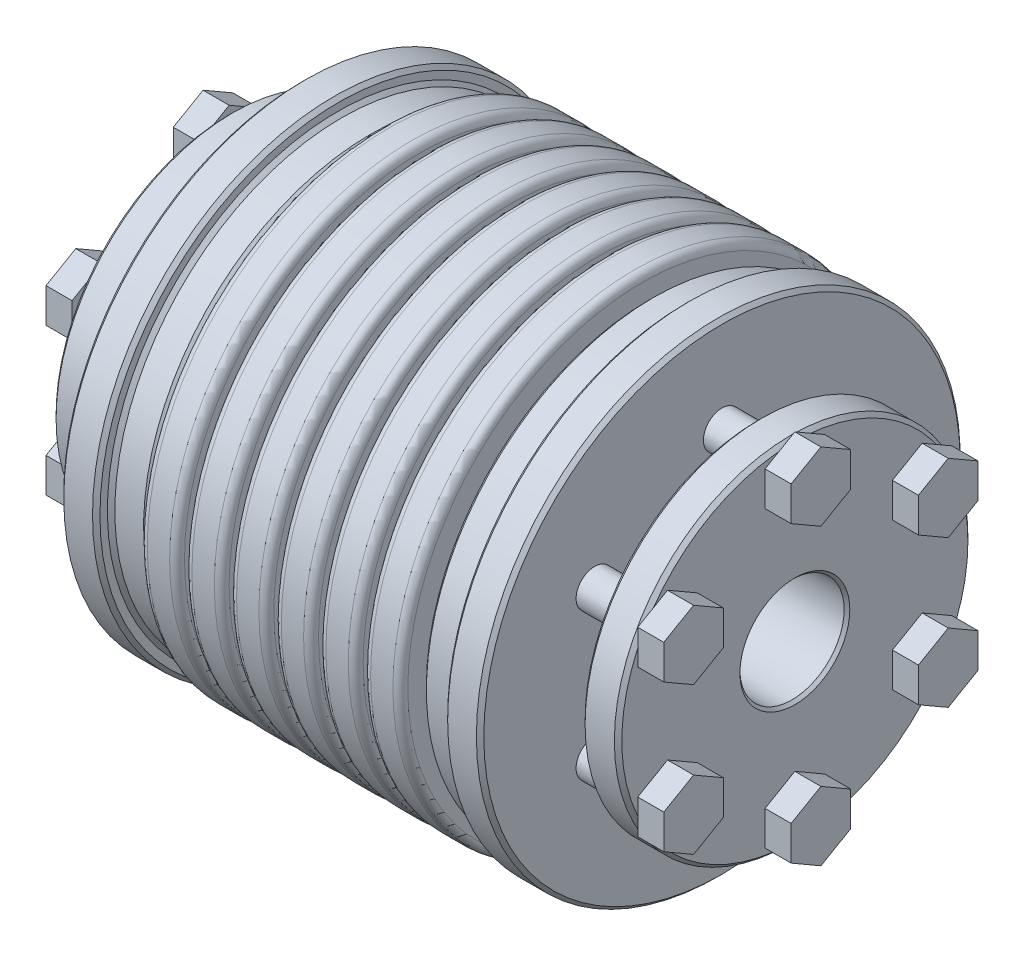
SolidWorks part; units mm, degrees
ref_plane "Front Plane" through (0, 0, 0) normal (0, 0, 1) x (1, 0, 0)
ref_plane "Top Plane" through (0, 0, 0) normal (0, 1, 0) x (1, 0, 0)
ref_plane "Right Plane" through (0, 0, 0) normal (1, 0, 0) x (0, 0, -1)
sketch "Sketch1" plane through (0, 0, 0) normal (1, 0, 0) x (0, 0, -1)
  circle A0 centre (0, 0) radius 32.5
  dimension "dim D" = 65
extrude "Boss-Extrude1" add sketch "Sketch1" along normal mid plane 76
sketch "Sketch2" plane through (38, 0, 0) normal (1, 0, 0) x (0, 0, -1)
  circle A0 centre (0, 0) radius 7
  dimension "dim d1" = 14
extrude "Cut-Extrude1" cut sketch "Sketch2" against normal blind 19
mirror "Mirror3" about plane through (0, 0, 0) normal (1, 0, 0) of "Cut-Extrude1"
chamfer "Chamfer1" distance 0.381 angle 45 4 edges at (-38, 0, -32.5) (38, 0, -32.5) (38, 0, -7) (-38, 0, -7)
ref_plane "L1" through (11, 0, 0) normal (1, 0, 0) x (0, 0, -1)
sketch "Sketch5" plane through (0, 0, 0) normal (1, 0, 0) x (0, 0, -1)
  line L0 (0, 7.381) -> (0, 32.5) construction
  circle A0 centre (0, 0) radius 7.381 construction
  circle A1 centre (0, 0) radius 19.9405
  circle A3 centre (0, 0) radius 32.5 construction
  point P9 (0, 19.9405)
extrude "Cut-Extrude2" cut sketch "Sketch5" against normal up to surface and the other way up to surface up to face at (-19, 0, -7) other way up to face at (19, 0, -7)
sketch "Sketch8" plane through (0, 0, 0) normal (0, 1, 0) x (1, 0, 0)
  line L0 (19, 19.9405) -> (-19, 19.9405) construction
  line L2 (-0.5, 21.9405) -> (0.5, 21.9405)
  line L3 (-0.5, 21.9405) -> (-0.5, 32.5)
  line L4 (-0.5, 32.5) -> (0.5, 32.5)
  line L5 (0, 21.9405) -> (0, 0) construction
  line L6 (0.5, 21.9405) -> (0.5, 32.5)
  line L7 (0, 0) -> (38, 0) construction
  line L8 (38, -32.119) -> (38, 32.119) construction
  line L9 (19, 7) -> (19, -7) construction
  line L10 (19, 7) -> (19, -7) construction
  line L11 (-38, -21.9405) -> (38, -21.9405) construction
  line L13 (0.5, 21.9405) -> (1.27, 21.9405) construction
  line L14 (-38, 32.119) -> (-38, -32.119) construction
  line L15 (5.5, 21.9405) -> (6.5, 21.9405)
  line L16 (5.5, 21.9405) -> (5.5, 32.5)
  line L17 (5.5, 32.5) -> (6.5, 32.5)
  line L18 (6.5, 21.9405) -> (6.5, 32.5)
  line L19 (11.5, 21.9405) -> (12.5, 21.9405)
  line L20 (11.5, 21.9405) -> (11.5, 32.5)
  line L21 (11.5, 32.5) -> (12.5, 32.5)
  line L22 (12.5, 21.9405) -> (12.5, 32.5)
  line L23 (17.5, 21.9405) -> (18.5, 21.9405)
  line L24 (17.5, 21.9405) -> (17.5, 32.5)
  line L25 (17.5, 32.5) -> (18.5, 32.5)
  line L26 (18.5, 21.9405) -> (18.5, 32.5)
  line L27 (-0.5, 21.9405) -> (5.5, 21.9405) construction
  line L28 (0, 0) -> (0, -21.9405) construction
  dimension "D2" = 4
  dimension "D1" = 1
  dimension "D3" = 2
  dimension "Dim L2" = 37
revolve "Cut-Revolve1" cut sketch "Sketch8" angle 360 about L7
mirror "Mirror2" about plane through (0, 0, 0) normal (1, 0, 0) of "Cut-Revolve1"
fillet "Fillet1" radius 1 14 edges at (0.5, 0, 32.5) (-0.5, 0, 32.5) (18.5, 0, 32.5) (17.5, 0, 32.5) (12.5, 0, 32.5) (11.5, 0, 32.5) (6.5, 0, 32.5) (5.5, 0, 32.5) (-17.5, 0, 32.5) (-12.5, 0, 32.5) (-11.5, 0, 32.5) (-6.5, 0, 32.5) (-5.5, 0, 32.5) (-18.5, 0, 32.5)
fillet "Fillet2" radius 0.25 14 edges at (-11.5, 0, 21.9405) (-5.5, 0, 21.9405) (0.5, 0, 21.9405) (6.5, 0, 21.9405) (12.5, 0, 21.9405) (18.5, 0, 21.9405) (17.5, 0, 21.9405) (11.5, 0, 21.9405) (5.5, 0, 21.9405) (-0.5, 0, 21.9405) (-6.5, 0, 21.9405) (-12.5, 0, 21.9405) (-17.5, 0, 21.9405) (-18.5, 0, 21.9405)
sketch "Sketch9" plane through (0, 0, 0) normal (0, 0, 1) x (1, 0, 0)
  line L0 (18.5, 30.5) -> (23.3563, 30.5)
  line L1 (18.5, 31.5) -> (18.5, -31.5) construction
  line L2 (23.3563, 30.5) -> (23.3563, 32.5)
  line L3 (37.619, 32.5) -> (19.5, 32.5) construction
  line L4 (23.3563, 32.5) -> (28.2125, 32.5)
  line L5 (28.2125, 32.5) -> (28.2125, 14.8937)
  line L6 (28.2125, 14.8937) -> (33.0688, 15.75)
  line L7 (33.0688, 15.75) -> (33.0688, 23.75)
  line L8 (33.0688, 23.75) -> (38, 23.75)
  line L9 (38, -32.119) -> (38, 32.119) construction
  line L10 (38, 23.75) -> (38, 37.5)
  line L11 (38, 37.5) -> (18.5, 37.5)
  line L12 (18.5, 37.5) -> (18.5, 30.5)
  line L13 (33.0688, 15.75) -> (28.2125, 15.75) construction
  line L14 (37.619, 7) -> (37.619, 32.5) construction
  line L15 (37.619, 19.75) -> (33.0688, 19.75) construction
  line L16 (38, 0) -> (-38, 0) construction
  line L17 (-38, 32.119) -> (-38, -32.119) construction
  line L18 (0, 0) -> (0, -27.1776) construction
  line L19 (-37.619, 19.75) -> (-33.0688, 19.75) construction
  line L20 (-37.619, 7) -> (-37.619, 32.5) construction
  line L21 (-33.0688, 15.75) -> (-28.2125, 15.75) construction
  line L22 (-18.5, 37.5) -> (-18.5, 30.5)
  line L23 (-38, 37.5) -> (-18.5, 37.5)
  line L24 (-38, 23.75) -> (-38, 37.5)
  line L25 (-33.0688, 23.75) -> (-38, 23.75)
  line L26 (-33.0688, 15.75) -> (-33.0688, 23.75)
  line L27 (-28.2125, 14.8937) -> (-33.0688, 15.75)
  line L28 (-28.2125, 32.5) -> (-28.2125, 14.8937)
  line L29 (-23.3563, 32.5) -> (-28.2125, 32.5)
  line L30 (-23.3563, 30.5) -> (-23.3563, 32.5)
  line L31 (-18.5, 30.5) -> (-23.3563, 30.5)
  dimension "D1" = 5
  dimension "D2" = 2
  dimension "D3" = 4
  dimension "D4" = 4
  dimension "D5" = 10
revolve "Cut-Revolve2" cut sketch "Sketch9" angle 360 about L16
sketch "Sketch10" plane through (38, 0, 0) normal (1, 0, 0) x (0, 0, -1)
  line L0 (0, 15.75) -> (0, 23.75) construction
  line L1 (13.104, 7.5656) -> (17.104, 5.2562)
  line L2 (0, 15.1312) -> (4, 17.4406)
  line L3 (4, 17.4406) -> (4, 22.0594)
  line L4 (4, 22.0594) -> (0, 24.3688)
  line L5 (0, 24.3688) -> (-4, 22.0594)
  line L6 (-4, 22.0594) -> (-4, 17.4406)
  line L7 (-4, 17.4406) -> (0, 15.1312)
  line L8 (17.104, 5.2562) -> (21.104, 7.5656)
  line L9 (21.104, 7.5656) -> (21.104, 12.1844)
  line L10 (21.104, 12.1844) -> (17.104, 14.4938)
  line L11 (17.104, 14.4938) -> (13.104, 12.1844)
  line L12 (13.104, 12.1844) -> (13.104, 7.5656)
  line L13 (13.6399, 7.875) -> (20.5681, 11.875) construction
  line L14 (13.104, -7.5656) -> (13.104, -12.1844)
  line L15 (13.104, -12.1844) -> (17.104, -14.4938)
  line L16 (17.104, -14.4938) -> (21.104, -12.1844)
  line L17 (21.104, -12.1844) -> (21.104, -7.5656)
  line L18 (21.104, -7.5656) -> (17.104, -5.2562)
  line L19 (17.104, -5.2562) -> (13.104, -7.5656)
  line L20 (13.6399, -7.875) -> (20.5681, -11.875) construction
  line L21 (0, -15.1312) -> (-4, -17.4406)
  line L22 (-4, -17.4406) -> (-4, -22.0594)
  line L23 (-4, -22.0594) -> (0, -24.3688)
  line L24 (0, -24.3688) -> (4, -22.0594)
  line L25 (4, -22.0594) -> (4, -17.4406)
  line L26 (4, -17.4406) -> (0, -15.1312)
  line L27 (0, -15.75) -> (0, -23.75) construction
  line L28 (-13.104, -7.5656) -> (-17.104, -5.2562)
  line L29 (-17.104, -5.2562) -> (-21.104, -7.5656)
  line L30 (-21.104, -7.5656) -> (-21.104, -12.1844)
  line L31 (-21.104, -12.1844) -> (-17.104, -14.4938)
  line L32 (-17.104, -14.4938) -> (-13.104, -12.1844)
  line L33 (-13.104, -12.1844) -> (-13.104, -7.5656)
  line L34 (-13.6399, -7.875) -> (-20.5681, -11.875) construction
  line L35 (-13.104, 7.5656) -> (-13.104, 12.1844)
  line L36 (-13.104, 12.1844) -> (-17.104, 14.4938)
  line L37 (-17.104, 14.4938) -> (-21.104, 12.1844)
  line L38 (-21.104, 12.1844) -> (-21.104, 7.5656)
  line L39 (-21.104, 7.5656) -> (-17.104, 5.2562)
  line L40 (-17.104, 5.2562) -> (-13.104, 7.5656)
  line L41 (-13.6399, 7.875) -> (-20.5681, 11.875) construction
  circle A0 centre (0, 0) radius 19.75 construction
  circle A1 centre (0, 0) radius 15.75 construction
  circle A2 centre (0, 0) radius 15.75 construction
  circle A3 centre (0, 0) radius 23.75 construction
  circle A4 centre (0, 19.75) radius 4 construction
  circle A5 centre (17.104, 9.875) radius 4 construction
  circle A6 centre (17.104, -9.875) radius 4 construction
  circle A7 centre (0, -19.75) radius 4 construction
  circle A8 centre (-17.104, -9.875) radius 4 construction
  circle A9 centre (-17.104, 9.875) radius 4 construction
  point P10 (0, 19.75)
  point P24 (17.104, 9.875)
  point P35 (17.104, -9.875)
  point P46 (0, -19.75)
  point P57 (-17.104, -9.875)
  point P68 (-17.104, 9.875)
  dimension "D1" = 6
  dimension "Dim Hex Head Width" = 8
extrude "Boss-Extrude2" add sketch "Sketch10" along normal blind 3.5 separate body
sketch "Sketch11" plane through (41.5, 0, 0) normal (1, 0, 0) x (0, 0, -1)
  line L0 (0, 24.3688) -> (0, 15.1312) construction
  line L1 (13.104, 7.5656) -> (21.104, 12.1844) construction
  circle A0 centre (0, 19.75) radius 2.5
  circle A1 centre (17.104, 9.875) radius 2.5
  circle A2 centre (17.104, -9.875) radius 2.5
  circle A3 centre (0, -19.75) radius 2.5
  circle A4 centre (-17.104, -9.875) radius 2.5
  circle A5 centre (-17.104, 9.875) radius 2.5
  dimension "D1" = 6
  dimension "Dim M" = 5
extrude "Boss-Extrude3" add sketch "Sketch11" against normal up to surface (13.2875 mm away) up to face at (28.2125, 14.8937, 0)
mirror "Mirror5" about plane through (0, 0, 0) normal (1, 0, 0) of bodies 123 124 125 126 127 128
chamfer "Chamfer2" distance 0.5 angle 45 12 edges at (33.0688, 23.75, 0) (38, 23.75, 0) (28.2125, 32.5, 0) (23.3563, 32.5, 0) (18.5, 30.5, 0) (23.3563, 30.5, 0) (-38, 23.75, 0) (-33.0688, 23.75, 0) (-28.2125, 32.5, 0) (-23.3563, 32.5, 0) (-23.3563, 30.5, 0) (-18.5, 30.5, 0)
